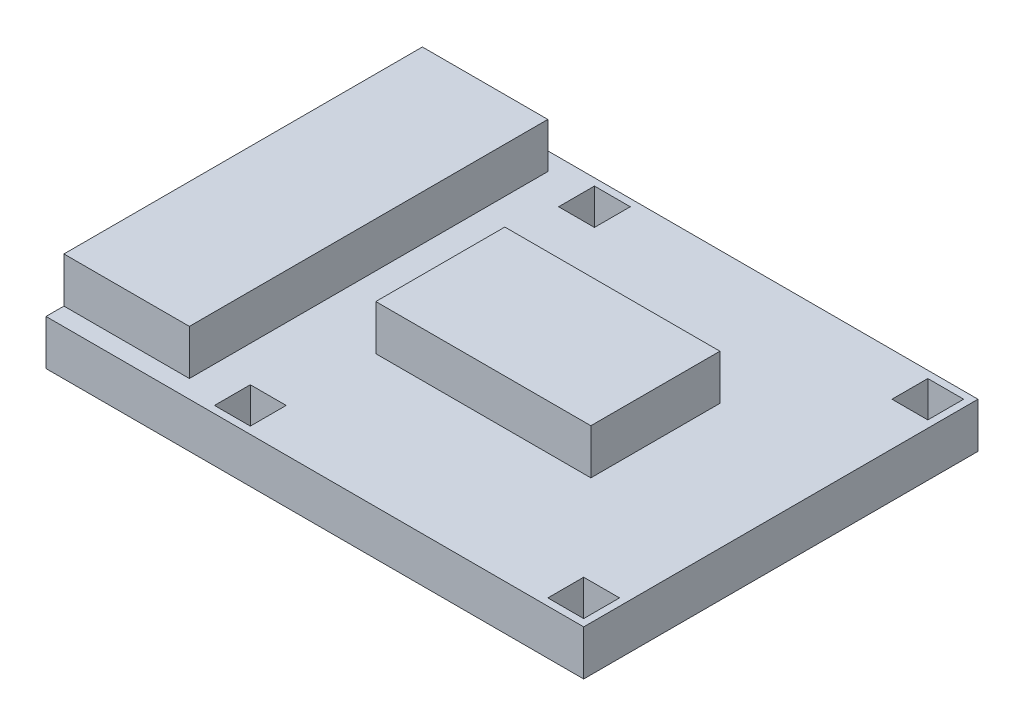
SolidWorks part; units mm, degrees
ref_plane "Front Plane" through (0, 0, 0) normal (0, 0, 1) x (1, 0, 0)
ref_plane "Top Plane" through (0, 0, 0) normal (0, 1, 0) x (1, 0, 0)
ref_plane "Right Plane" through (0, 0, 0) normal (1, 0, 0) x (0, 0, -1)
sketch "Sketch1" plane through (0, 0, 0) normal (0, 1, 0) x (1, 0, 0)
  line L1 (0, 0) -> (150, 0)
  line L2 (0, 0) -> (0, 110)
  line L3 (0, 110) -> (150, 110)
  line L4 (150, 0) -> (150, 110)
  dimension "D1" = 150
  dimension "D2" = 110
extrude "Boss-Extrude1" add sketch "Sketch1" along normal blind 1.6
sketch "Sketch2" plane through (0, 1.6, 0) normal (0, 1, 0) x (1, 0, 0)
  line L0 (0, 0) -> (150, 0) construction
  line L1 (150, 0) -> (150, 110) construction
  line L2 (150, 110) -> (0, 110) construction
  line L3 (0, 110) -> (0, 0) construction
  line L5 (45, 108) -> (55, 108)
  line L6 (45, 108) -> (45, 98)
  line L7 (45, 98) -> (55, 98)
  line L8 (55, 108) -> (55, 98)
  line L9 (45, 108) -> (55, 98) construction
  line L10 (45, 98) -> (55, 108) construction
  line L11 (148, 108) -> (138, 108)
  line L12 (148, 108) -> (148, 98)
  line L13 (148, 98) -> (138, 98)
  line L14 (138, 108) -> (138, 98)
  line L15 (148, 108) -> (138, 98) construction
  line L16 (148, 98) -> (138, 108) construction
  line L17 (148, 2) -> (138, 2)
  line L18 (148, 2) -> (148, 12)
  line L19 (148, 12) -> (138, 12)
  line L20 (138, 2) -> (138, 12)
  line L21 (148, 2) -> (138, 12) construction
  line L22 (148, 12) -> (138, 2) construction
  line L23 (45, 2) -> (55, 2)
  line L24 (45, 2) -> (45, 12)
  line L25 (45, 12) -> (55, 12)
  line L26 (55, 2) -> (55, 12)
  line L27 (45, 2) -> (55, 12) construction
  line L28 (45, 12) -> (55, 2) construction
  line L29 (0, 110) -> (150, 110)
  line L30 (0, 110) -> (0, 0)
  line L31 (0, 0) -> (150, 0)
  line L32 (150, 110) -> (150, 0)
  point P0 (50, 103)
  point P1 (143, 103)
  point P2 (143, 7)
  point P3 (50, 7)
  point P4 (50, 103)
  point P9 (143, 103)
  point P22 (143, 7)
  point P27 (50, 7)
  dimension "D1" = 7
  dimension "D2" = 7
  dimension "D3" = 7
  dimension "D4" = 50
  dimension "D5" = 10
extrude "Boss-Extrude2" add sketch "Sketch2" along normal blind 11
hole_wizard "Ø4.0 (4.3) Diameter Hole1" positions "Sketch6" profile "Sketch7" hole size "Ø4.0" standard "ANSI Metric" end condition through all
sketch "Sketch6" plane through (0, 1.6, 0) normal (0, 1, 0) x (1, 0, 0)
  line L0 (45, 108) -> (55, 98) construction
  point P2 (143, 103)
  point P5 (50, 103)
  point P9 (50, 7)
  point P12 (143, 7)
sketch "Sketch7" plane through (143, 1.6, -103) normal (1, 0, 0) x (0, 0, 1)
  line L0 (0, 0) -> (0, 1.6)
  line L1 (0, 1.6) -> (2.15, 1.6)
  line L2 (2.15, 1.6) -> (2.15, 0)
  line L5 (2.15, 0) -> (0, 0)
  line L11 (0, -6.35) -> (0, 107.95) construction
  dimension "Thru Hole Dia." = 4.3
  dimension "Thru Hole Depth" = 1.6
sketch "Sketch3" plane through (0, 12.6, 0) normal (0, 1, 0) x (1, 0, 0)
  line L0 (0, 55) -> (150, 55) construction
  line L1 (0, 110) -> (0, 0) construction
  line L2 (150, 0) -> (150, 110) construction
  line L4 (0, 105) -> (35, 105)
  line L5 (0, 105) -> (0, 5)
  line L6 (0, 5) -> (35, 5)
  line L7 (35, 105) -> (35, 5)
  point P10 (35, 55)
  dimension "D1" = 100
  dimension "D2" = 35
extrude "Boss-Extrude3" add sketch "Sketch3" along normal blind 12.6
sketch "Sketch4" plane through (0, 12.6, 0) normal (0, 1, 0) x (1, 0, 0)
  line L0 (150, 0) -> (150, 110) construction
  line L1 (55, 73) -> (115, 73)
  line L2 (55, 73) -> (55, 37)
  line L3 (55, 37) -> (115, 37)
  line L4 (115, 73) -> (115, 37)
  line L5 (0, 105) -> (0, 5) construction
  line L6 (150, 110) -> (0, 110) construction
  line L7 (0, 0) -> (150, 0) construction
  dimension "D1" = 35
  dimension "D2" = 55
  dimension "D3" = 37
  dimension "D4" = 37
extrude "Boss-Extrude4" add sketch "Sketch4" along normal up to surface (12.6 mm away) up to face at (17.5, 25.2, -55)
sketch "Sketch5" plane through (0, 12.6, 0) normal (0, 1, 0) x (1, 0, 0)
  line L0 (0, 105) -> (0, 5) construction
  line L1 (150, 110) -> (0, 110) construction
  point P0 (40, 102.5)
  point P1 (112, 102.5)
  point P2 (112, 96)
  point P3 (121, 102.5)
  point P4 (117, 82)
  point P5 (145, 52)
  point P6 (145, 18)
  dimension "D1" = 40
  dimension "D2" = 7.5
  dimension "D3" = 112
  dimension "D4" = 7.5
  dimension "D5" = 14
  dimension "D6" = 121
  dimension "D7" = 28
  dimension "D8" = 117
  dimension "D9" = 145
  dimension "D10" = 58
  dimension "D11" = 92
